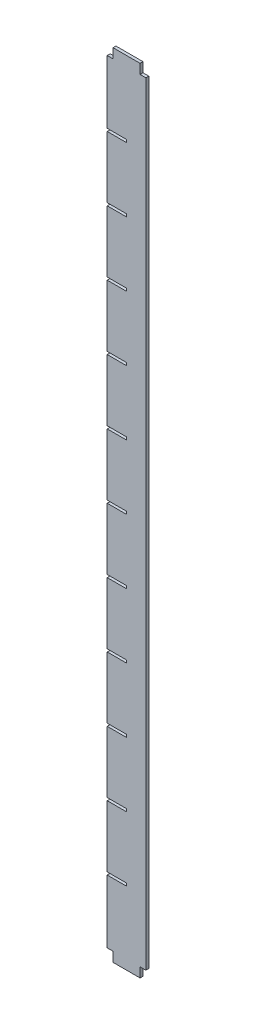
SolidWorks part; units mm, degrees
ref_plane "前视基准面" through (0, 0, 0) normal (0, 0, 1) x (1, 0, 0)
ref_plane "上视基准面" through (0, 0, 0) normal (0, 1, 0) x (1, 0, 0)
ref_plane "右视基准面" through (0, 0, 0) normal (1, 0, 0) x (0, 0, -1)
sketch "草图1" plane through (0, 0, 0) normal (0, 0, 1) x (1, 0, 0)
  line L1 (-10, -205) -> (10, -205)
  line L2 (-10, -205) -> (-10, 205)
  line L3 (-10, 205) -> (10, 205)
  line L4 (10, -205) -> (10, 205)
  line L5 (-10, -205) -> (10, 205) construction
  line L6 (-10, 205) -> (10, -205) construction
  point P0 (0, 0)
  dimension "D1" = 410
  dimension "D2" = 20
extrude "凸台-拉伸1" add sketch "草图1" along normal blind 1.5
sketch "草图2" plane through (0, 0, 1.5) normal (0, 0, 1) x (1, 0, 0)
  line L1 (-10, 205) -> (-7, 205)
  line L2 (-10, 205) -> (-10, 200)
  line L3 (-10, 200) -> (-7, 200)
  line L4 (-7, 205) -> (-7, 200)
  line L5 (-10, 205) -> (-7, 200) construction
  line L6 (-10, 200) -> (-7, 205) construction
  line L7 (10, 205) -> (7, 205)
  line L8 (10, 205) -> (10, 200)
  line L9 (10, 200) -> (7, 200)
  line L10 (7, 205) -> (7, 200)
  line L11 (10, 205) -> (7, 200) construction
  line L12 (10, 200) -> (7, 205) construction
  line L13 (-10, -205) -> (-7, -205)
  line L14 (-10, -205) -> (-10, -200)
  line L15 (-10, -200) -> (-7, -200)
  line L16 (-7, -205) -> (-7, -200)
  line L17 (-10, -205) -> (-7, -200) construction
  line L18 (-10, -200) -> (-7, -205) construction
  line L19 (10, -205) -> (7, -205)
  line L20 (10, -205) -> (10, -200)
  line L21 (10, -200) -> (7, -200)
  line L22 (7, -205) -> (7, -200)
  line L23 (10, -205) -> (7, -200) construction
  line L24 (10, -200) -> (7, -205) construction
  point P4 (-8.5, 202.5)
  point P10 (8.5, 202.5)
  point P16 (-8.5, -202.5)
  point P22 (8.5, -202.5)
  dimension "D1" = 5
  dimension "D2" = 5
  dimension "D3" = 3
  dimension "D4" = 3
  dimension "D5" = 5
  dimension "D6" = 5
  dimension "D7" = 3
  dimension "D8" = 3
extrude "切除-拉伸1" cut sketch "草图2" against normal up to next
sketch "草图3" plane through (0, 0, 1.5) normal (0, 0, 1) x (1, 0, 0)
  line L0 (-20, -0.7) -> (0, -0.7)
  line L1 (-20, -0.7) -> (-20, 0.7)
  line L2 (0, -0.7) -> (0, 0.7)
  line L3 (-20, 0.7) -> (0, 0.7)
  line L4 (-20, -0.7) -> (0, 0.7) construction
  line L5 (0, -0.7) -> (-20, 0.7) construction
  line L6 (-10, 200) -> (-10, -200) construction
  point P1 (-10, 0)
  dimension "D1" = 1.4
  dimension "D2" = 10
extrude "切除-拉伸2" cut sketch "草图3" against normal up to next (1.5 mm away)
pattern_linear "阵列(线性)1" count 6 spacing 33.33 along (0, 1, 0) count 6 spacing 33.33 along (0, -1, 0) of "切除-拉伸2"
